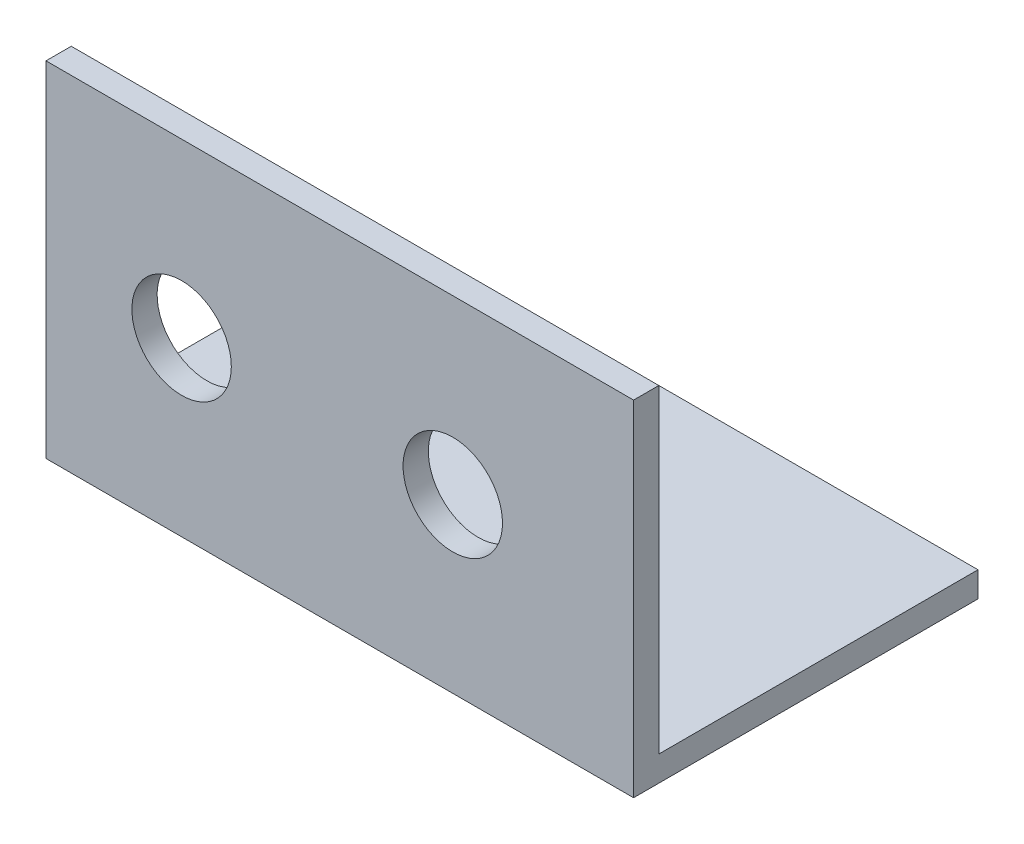
SolidWorks part; units mm, degrees
ref_plane "Front Plane" through (0, 0, 0) normal (0, 0, 1) x (1, 0, 0)
ref_plane "Top Plane" through (0, 0, 0) normal (0, 1, 0) x (1, 0, 0)
ref_plane "Right Plane" through (0, 0, 0) normal (1, 0, 0) x (0, 0, -1)
sketch "Sketch1" plane through (0, 0, 0) normal (1, 0, 0) x (0, 0, -1)
  line L0 (0, 35.306) -> (0, 0)
  line L1 (0, 0) -> (35.306, 0)
  line L2 (35.306, 0) -> (35.306, -2.794)
  line L3 (35.306, -2.794) -> (-2.794, -2.794)
  line L4 (-2.794, -2.794) -> (-2.794, 35.306)
  line L5 (0, 35.306) -> (-2.794, 35.306)
  dimension "D1" = 2.794
  dimension "D2" = 38.1
  dimension "D3" = 38.1
extrude "Boss-Extrude1" add sketch "Sketch1" along normal blind 65
sketch "Sketch2" plane through (0, 0, 2.794) normal (0, 0, 1) x (1, 0, 0)
  line L1 (65, -2.794) -> (0, -2.794) construction
  line L2 (0, 35.306) -> (0, -2.794) construction
  line L3 (65, 35.306) -> (65, -2.794) construction
  circle A0 centre (15, 16.256) radius 5.5
  circle A1 centre (45, 16.256) radius 5.5
  dimension "D1" = 15
  dimension "D2" = 19.05
  dimension "D3" = 11
  dimension "D4" = 20
extrude "Cut-Extrude1" cut sketch "Sketch2" against normal blind 65
